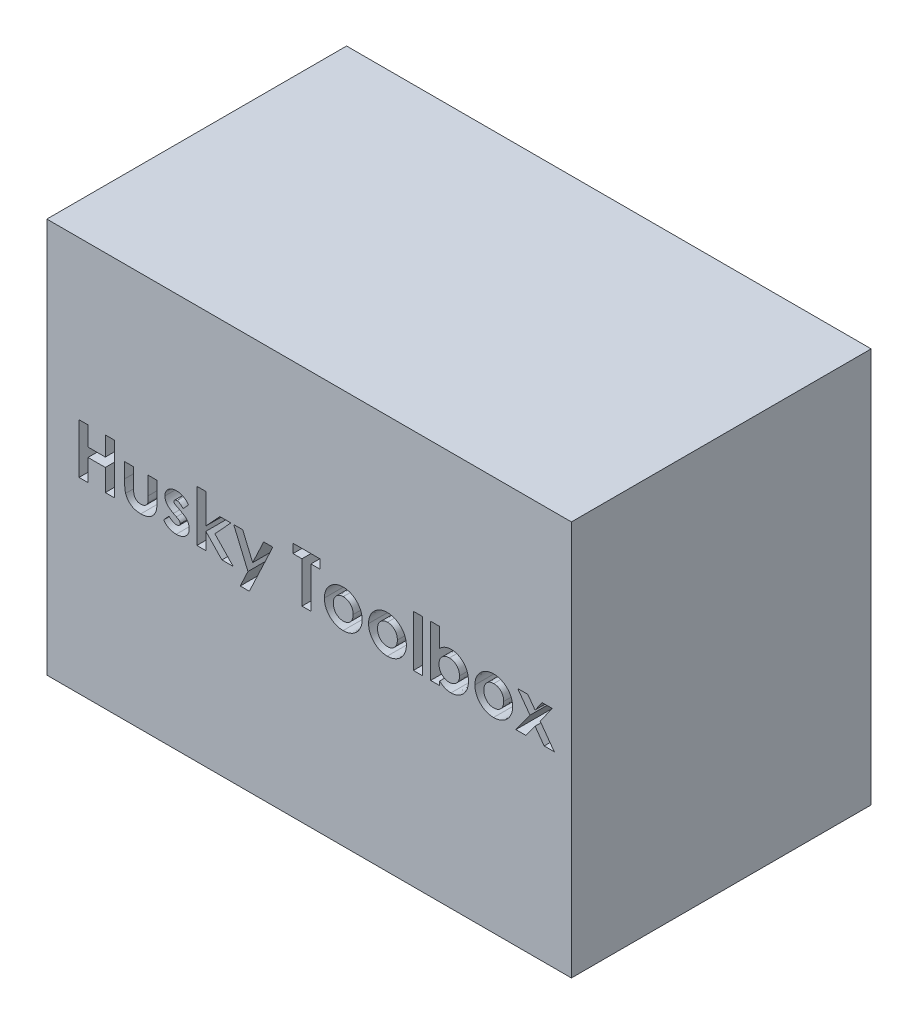
SolidWorks part; units mm, degrees
ref_plane "Front Plane" through (0, 0, 0) normal (0, 0, 1) x (1, 0, 0)
ref_plane "Top Plane" through (0, 0, 0) normal (0, 1, 0) x (1, 0, 0)
ref_plane "Right Plane" through (0, 0, 0) normal (1, 0, 0) x (0, 0, -1)
sketch "Sketch1" plane through (0, 0, 0) normal (0, 1, 0) x (1, 0, 0)
  line L1 (-533.4, -304.8) -> (533.4, -304.8)
  line L2 (-533.4, -304.8) -> (-533.4, 304.8)
  line L3 (-533.4, 304.8) -> (533.4, 304.8)
  line L4 (533.4, -304.8) -> (533.4, 304.8)
  line L5 (-533.4, -304.8) -> (533.4, 304.8) construction
  line L6 (-533.4, 304.8) -> (533.4, -304.8) construction
  point P0 (0, 0)
  dimension "D1" = 1066.8
  dimension "D2" = 609.6
extrude "Boss-Extrude1" add sketch "Sketch1" along normal blind 803.275
sketch "Sketch2" plane through (0, 0, 304.8) normal (0, 0, 1) x (1, 0, 0)
  line L0 (-533.4, 0) -> (533.4, 0) construction
  text T0 "<b>Husky Toolbox</b>" font "Century Gothic" height 101.6
  dimension "D1" = 381
extrude "Cut-Extrude1" cut sketch "Sketch2" against normal blind 76.2
